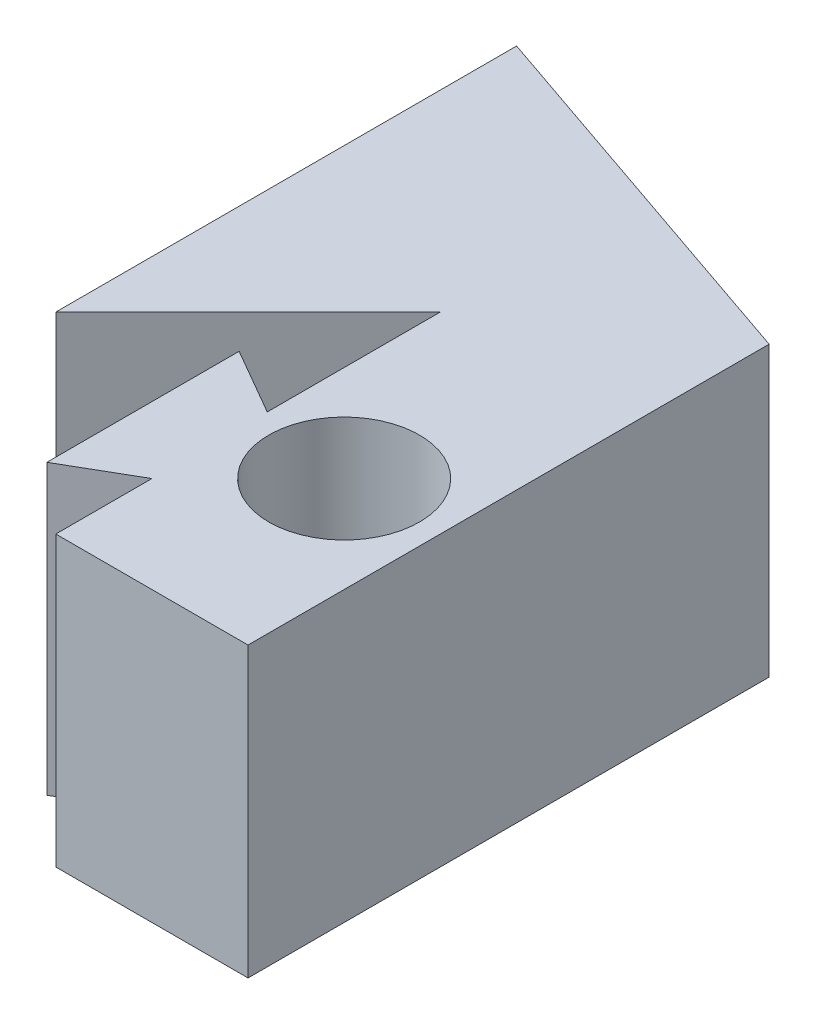
SolidWorks part; units mm, degrees
ref_plane "Front Plane" through (0, 0, 0) normal (0, 0, 1) x (1, 0, 0)
ref_plane "Top Plane" through (0, 0, 0) normal (0, 1, 0) x (1, 0, 0)
ref_plane "Right Plane" through (0, 0, 0) normal (1, 0, 0) x (0, 0, -1)
sketch "Sketch2" plane through (0, 0, 0) normal (0, 1, 0) x (1, 0, 0)
  line L0 (0, 0) -> (-3.175, 0) construction
  line L1 (0, 0) -> (0, 9.525) construction
  line L2 (-3.175, 6.35) -> (-3.175, 12.7)
  line L3 (-3.175, 12.7) -> (9.525, 12.7)
  line L4 (3.175, 6.985) -> (3.175, 12.7)
  line L5 (0.9753, 8.255) -> (3.175, 6.985)
  line L6 (0.9753, 8.255) -> (0.9753, 1.905)
  line L7 (3.175, 3.175) -> (3.175, 0)
  line L8 (3.175, 0) -> (9.525, 0)
  line L9 (9.525, 0) -> (9.525, 12.7)
  line L10 (3.175, 12.7) -> (3.175, 6.985)
  line L11 (0.9753, 8.255) -> (0.9753, 1.905)
  line L12 (3.175, 3.175) -> (0.9753, 1.905)
  line L13 (3.175, 3.175) -> (3.175, 0)
  line L14 (3.175, 0) -> (3.175, 12.7)
  circle A0 centre (6.35, 6.35) radius 2.4892
  line B0 (-3.175, 6.35) -> (-3.175, 0)
  line B1 (-3.175, 0) -> (3.175, 0)
  line B2 (3.175, 0) -> (3.175, 3.175)
  line B3 (3.175, 3.175) -> (0.9753, 1.905)
  line B4 (0.9753, 1.905) -> (0.9753, 8.255)
  line B5 (0.9753, 8.255) -> (3.175, 6.985)
  line B6 (3.175, 6.985) -> (3.175, 12.7)
  line B7 (3.175, 12.7) -> (-3.175, 6.35)
  dimension "D3" = 4.9784
  dimension "D1" = 3.175
  dimension "D2" = 12.7
  dimension "D4" = 6.35
  dimension "D5" = 3.175
sketch_block_instance "Forks-1"
sketch_block "Forks"
extrude "Boss-Extrude3" add sketch "Sketch2" along normal blind 9.525 contours A0
sketch "Sketch3" plane through (0, 9.525, 0) normal (0, 1, 0) x (1, 0, 0)
  line L0 (-3.175, 6.35) -> (-3.175, 12.7)
  line L1 (-3.175, 12.7) -> (9.525, 12.7)
  line L2 (9.525, 12.7) -> (9.525, 0)
  line L3 (9.525, 0) -> (-3.175, 0)
  line L4 (-3.175, 0) -> (-3.175, 6.35)
  line L5 (-3.175, 6.35) -> (3.175, 12.7)
  line L6 (3.175, 12.7) -> (3.175, 6.985)
  line L7 (3.175, 6.985) -> (0.9753, 8.255)
  line L8 (0.9753, 8.255) -> (0.9753, 1.905)
  line L9 (0.9753, 1.905) -> (3.175, 3.175)
  line L10 (3.175, 3.175) -> (3.175, 0)
  circle M1 centre (6.35, 6.35) radius 2.4892
extrude "Boss-Extrude4" add sketch "Sketch3" against normal up to surface (9.525 mm away) contours L9 L10 L3 L2 L1 L6 L7 L8 M1 | L0 L5 L1 up to face at (6.35, 0, -3.8608)
sketch "Sketch4" plane through (0, 9.525, 0) normal (0, 1, 0) x (1, 0, 0)
  line L0 (9.525, 0) -> (9.525, 12.7) construction
  line L1 (-3.175, 12.7) -> (9.525, 12.7)
  line L2 (-3.175, 12.7) -> (-3.175, 13.97)
  line L3 (-3.175, 13.97) -> (9.525, 13.97)
  line L4 (9.525, 12.7) -> (9.525, 13.97)
  dimension "D1" = 1.27
extrude "Boss-Extrude5" add sketch "Sketch4" against normal up to surface (9.525 mm away) up to face at (4.2126, 0, -5.715)
sketch "Sketch5" plane through (0, 9.525, 0) normal (0, 1, 0) x (1, 0, 0)
  circle A0 centre (6.35, 6.35) radius 2.4892
extrude "Cut-Extrude1" cut sketch "Sketch5" against normal through all both and the other way through all
sketch "Sketch7" plane through (0, 9.525, 0) normal (0, 1, 0) x (1, 0, 0)
  line L0 (9.525, 13.97) -> (-3.175, 13.97) construction
  point P0 (9.2506, 16.5956)
  line B0 (9.525, 13.97) -> (9.525, 17.2125)
  line B1 (9.525, 17.2125) -> (-3.175, 21.5712)
  line B2 (-3.175, 21.5712) -> (-3.175, 13.97)
  line B3 (-3.175, 13.97) -> (9.525, 13.97)
sketch_block_instance "other mount for thing-3"
sketch_block "other mount for thing"
extrude "Boss-Extrude7" add sketch "Sketch7" against normal up to surface (9.525 mm away) up to face at (6.35, 0, -3.8608)
